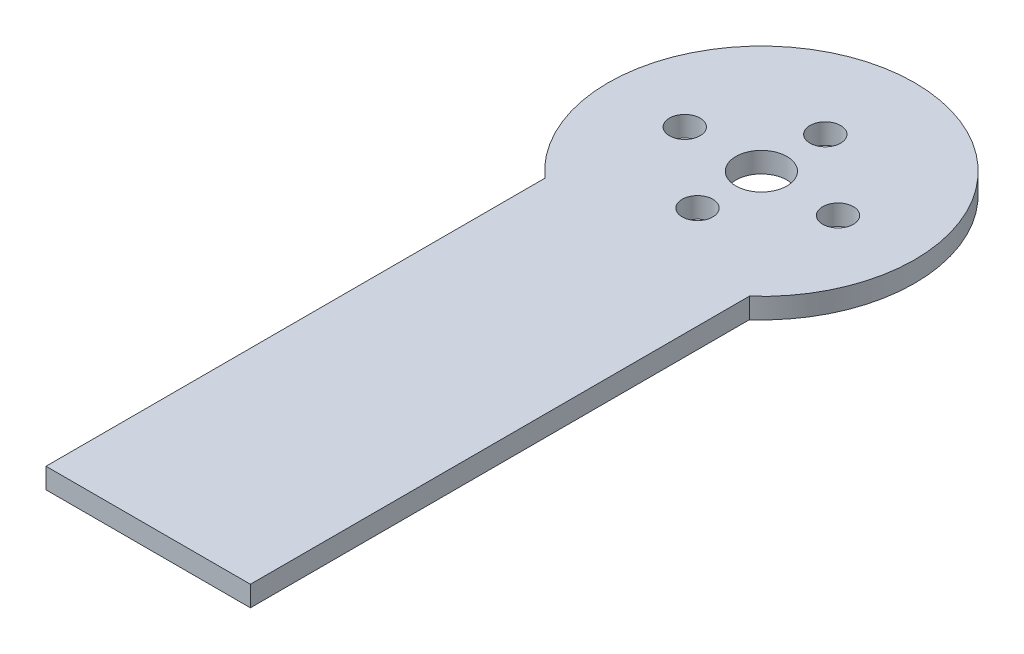
SolidWorks part; units mm, degrees
ref_plane "Front Plane" through (0, 0, 0) normal (0, 0, 1) x (1, 0, 0)
ref_plane "Top Plane" through (0, 0, 0) normal (0, 1, 0) x (1, 0, 0)
ref_plane "Right Plane" through (0, 0, 0) normal (1, 0, 0) x (0, 0, -1)
sketch "Sketch1" plane through (0, 0, 0) normal (0, 1, 0) x (1, 0, 0)
  line L0 (0, 7.9375) -> (0, -7.9375) construction
  line L1 (9.525, 0) -> (-9.525, 0) construction
  line L2 (12.7, 0) -> (-12.7, 0) construction
  line L3 (-12.7, -14.199) -> (-12.7, -76.2)
  line L4 (-12.7, -76.2) -> (12.7, -76.2)
  line L5 (12.7, -76.2) -> (12.7, -14.199)
  circle A0 centre (0, 0) radius 19.05
  circle A1 centre (-9.525, 0) radius 1.905
  circle A2 centre (0, 7.9375) radius 1.905
  circle A3 centre (9.525, 0) radius 1.905
  circle A4 centre (0, -7.9375) radius 1.905
  circle A5 centre (0, 0) radius 3.175
  point P6 (0, 0)
  point P9 (0, 0)
  point P16 (0, 0)
  dimension "D1" = 38.1
  dimension "D4" = 3.81
  dimension "D7" = 6.35
  dimension "D2" = 15.875
  dimension "D3" = 19.05
  dimension "D5" = 25.4
  dimension "D6" = 76.2
extrude "Boss-Extrude1" add sketch "Sketch1" along normal blind 2.54 contours A0 A4 A3 A2 A1 | A0 L3 L4 L5
